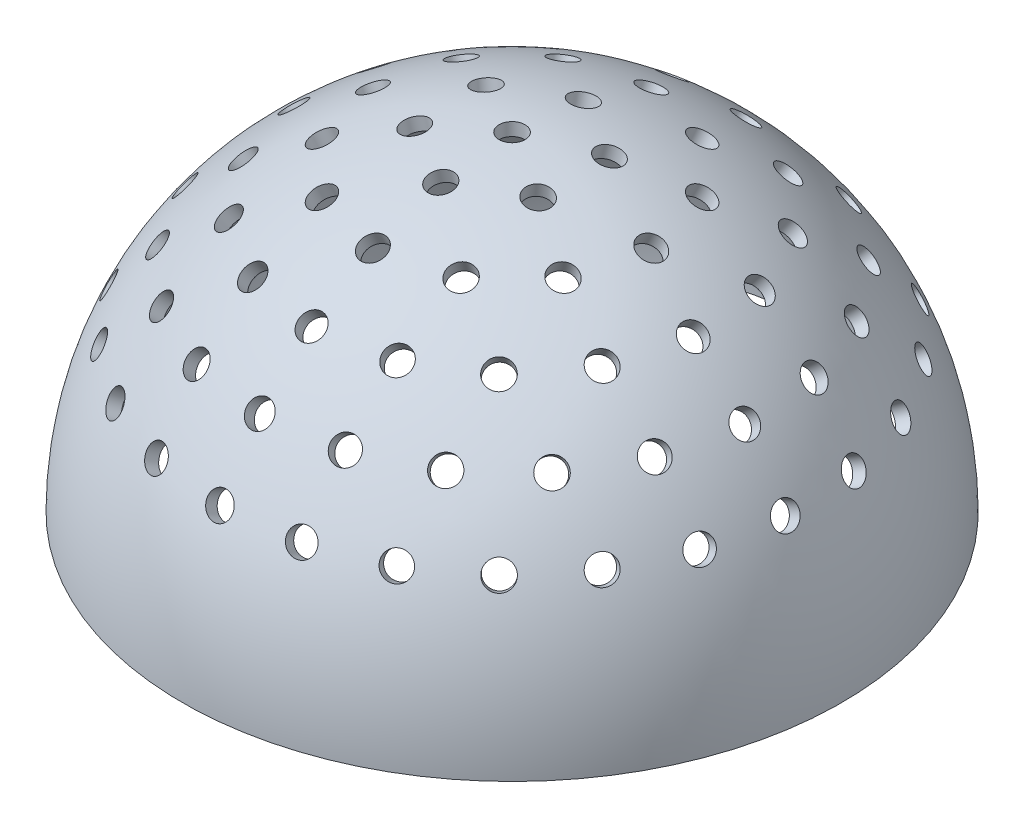
SolidWorks part; units mm, degrees
ref_plane "Front Plane" through (0, 0, 0) normal (0, 0, 1) x (1, 0, 0)
ref_plane "Top Plane" through (0, 0, 0) normal (0, 1, 0) x (1, 0, 0)
ref_plane "Right Plane" through (0, 0, 0) normal (1, 0, 0) x (0, 0, -1)
sketch "Sketch1" plane through (0, 0, 0) normal (0, 0, 1) x (1, 0, 0)
  line L0 (0, 0) -> (0, 12.7)
  line L1 (0, 0) -> (12.7, 0)
  arc A0 (0, 12.7) -> (12.7, 0) centre (0, 0) cw
  dimension "D1" = 12.7
  dimension "D2" = 12.7
revolve "Revolve1" add sketch "Sketch1" angle 360 about L0
sketch "Sketch2" plane through (0, 0, 0) normal (0, 0, 1) x (1, 0, 0)
  line L0 (0, 0) -> (0, 12.2)
  line L1 (0, 0) -> (12.2, 0)
  line L2 (-12.7, 0) -> (12.7, 0) construction
  arc A0 (0, 12.2) -> (12.2, 0) centre (0, 0) cw
  dimension "D1" = 12.2
  dimension "D2" = 12.2
revolve "Cut-Revolve1" cut sketch "Sketch2" angle 360 about L0
sketch "Sketch3" plane through (0, 0, 0) normal (0, 1, 0) x (1, 0, 0)
  circle A0 centre (0, 0) radius 0.5
  dimension "D1" = 1
extrude "Cut-Extrude1" cut sketch "Sketch3" along normal through all
pattern_circular "CirPattern1" count 2 every 12.5 about axis through (0, 0, 0) along (1, 0, 0) of "Cut-Extrude1"
pattern_circular "CirPattern2" count 6 over 360 about axis through (0, 0, 0) along (0, 1, 0) of "CirPattern1"
pattern_circular "CirPattern3" count 2 every 25 about axis through (0, 0, 0) along (1, 0, 0) of "Cut-Extrude1"
pattern_circular "CirPattern4" count 2 every 37.5 about axis through (0, 0, 0) along (1, 0, 0) of "Cut-Extrude1"
pattern_circular "CirPattern5" count 2 every 50 about axis through (0, 0, 0) along (1, 0, 0) of "Cut-Extrude1"
pattern_circular "CirPattern6" count 2 every 62.5 about axis through (0, 0, 0) along (1, 0, 0) of "Cut-Extrude1"
pattern_circular "CirPattern7" count 12 over 360 about axis through (0, 0, 0) along (0, 1, 0) of "CirPattern3"
pattern_circular "CirPattern8" count 17 over 360 about axis through (0, 0, 0) along (0, 1, 0) of "CirPattern4"
pattern_circular "CirPattern9" count 21 over 360 about axis through (0, 0, 0) along (0, 1, 0) of "CirPattern5"
pattern_circular "CirPattern10" count 25 over 360 about axis through (0, 0, 0) along (0, 1, 0) of "CirPattern6"
equation "\"D1@Sketch1\"=\"dia_outer_out\"+\"tolerance_domes\"/2"
equation "\"D2@Sketch1\"=\"dia_outer_out\"+\"tolerance_domes\"/2"
equation "\"D1@Sketch2\"=\"dia_outer_in\"+\"tolerance_domes\"/2"
equation "\"D2@Sketch2\"=\"dia_outer_in\"+\"tolerance_domes\"/2"
equation "\"D1@Sketch3\"=\"d_marker\""
equation "\"D2@CirPattern1\"=\"degrees\""
equation "\"D1@CirPattern2\" = \"n_markers_1\""
equation "\"D2@CirPattern3\"=2*\"degrees\""
equation "\"D2@CirPattern4\"=3*\"degrees\""
equation "\"D2@CirPattern5\"=4*\"degrees\""
equation "\"D2@CirPattern6\"=5*\"degrees\""
equation "\"D1@CirPattern7\" = \"n_markers_2\""
equation "\"D1@CirPattern8\"= \"n_markers_3\""
equation "\"D1@CirPattern9\" = \"n_markers_4\""
equation "\"D1@CirPattern10\" = \"n_markers_5\""
equation "\"dia_difflayer\"= 13"
equation "\"dia_outer_out\"= 12.5"
equation "\"dia_outer_in\"= 12"
equation "\"dia_inner_out\"= 11"
equation "\"dia_inner_in\"= 10.5"
equation "\"degrees\"= 12.5"
equation "\"d_marker\"= 1"
equation "\"t_marker\"= 0.5"
equation "\"n_markers_1\"= 6"
equation "\"n_markers_2\"= round ( 6 * sin ( 2*\"degrees\" ) / sin ( \"degrees\" ) )"
equation "\"n_markers_3\"= round ( 6 * sin ( 3*\"degrees\" ) / sin ( \"degrees\" ) )"
equation "\"n_markers_4\"= round ( 6 * sin ( 4*\"degrees\" ) / sin ( \"degrees\" ) )"
equation "\"n_markers_5\"= round ( 6 * sin ( 5*\"degrees\" ) / sin ( \"degrees\" ) )"
equation "\"n_teeth\"= 8"
equation "\"tolerance_domes\"= 0.4"
equation "\"tolerance_large\"= 0.4"
equation "\"pinhole_slot\"= 3.8"
